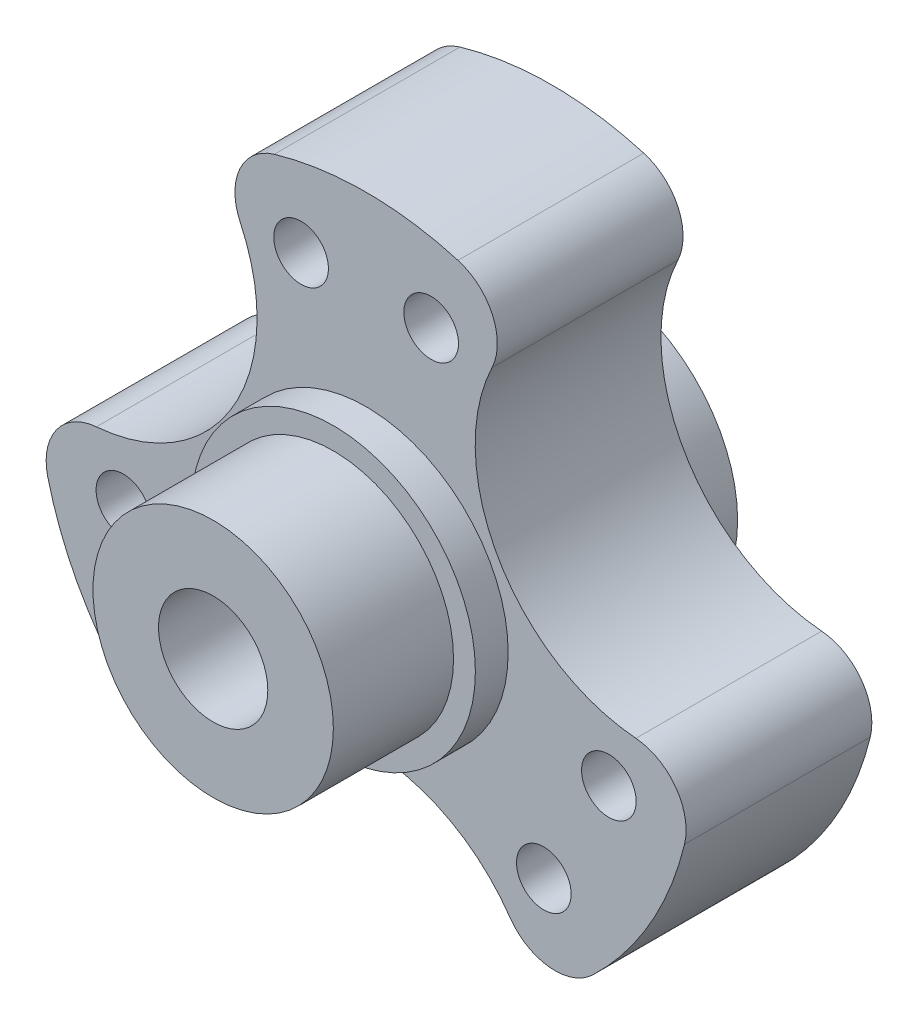
SolidWorks part; units mm, degrees
material "TIMETAL 35A CP 钛 (ASTM 等级 1) 99.1 Ti"
ref_plane "前视基准面" through (0, 0, 0) normal (0, 0, 1) x (1, 0, 0)
ref_plane "上视基准面" through (0, 0, 0) normal (0, 1, 0) x (1, 0, 0)
ref_plane "右视基准面" through (0, 0, 0) normal (1, 0, 0) x (0, 0, -1)
sketch "草图1" plane through (0, 0, 0) normal (0, 0, 1) x (1, 0, 0)
  line L0 (0, -38.5528) -> (0, 39.6388) construction
  line L1 (0, 0) -> (-10.2324, 38.188) construction
  line L2 (5.9528, 22.2163) -> (0, 0) construction
  circle A0 centre (0, 0) radius 23 construction
  circle A1 centre (-5.9528, 22.2163) radius 2.5
  circle A2 centre (0, 0) radius 30
  circle A3 centre (5.9528, 22.2163) radius 2.5
  circle A4 centre (22.2163, -5.9528) radius 2.5
  circle A5 centre (16.2635, -16.2635) radius 2.5
  circle A6 centre (-16.2635, -16.2635) radius 2.5
  circle A7 centre (-22.2163, -5.9528) radius 2.5
  point P22 (0, 0)
  dimension "D1" = 46
  dimension "D2" = 15
  dimension "D3" = 60
  dimension "D5" = 5
  dimension "D6" = 5
  dimension "D4" = 15
  dimension "D7" = 23
  dimension "D8" = 23
  dimension "D9" = 3
extrude "凸台-拉伸1" add sketch "草图1" along normal blind 17
sketch "草图2" plane through (0, 0, 17) normal (0, 0, 1) x (1, 0, 0)
  line L0 (0, 0) -> (25.9808, 15) construction
  line L1 (0, 0) -> (0, 30) construction
  circle A0 centre (0, 0) radius 30 construction
  circle A1 centre (25.9808, 15) radius 16
  dimension "D2" = 32
  dimension "D1" = 60
extrude "切除-拉伸1" cut sketch "草图2" against normal through all
pattern_circular "阵列(圆周)1" count 3 over 360 about axis through (0, 0, 0) along (0, 0, 1) of "切除-拉伸1"
sketch "草图4" plane through (0, 0, 17) normal (0, 0, 1) x (1, 0, 0)
  circle A0 centre (0, 0) radius 11
  dimension "D1" = 22
extrude "凸台-拉伸3" add sketch "草图4" along normal blind 14
sketch "草图5" plane through (0, 0, 31) normal (0, 0, 1) x (1, 0, 0)
  circle A0 centre (0, 0) radius 5
  dimension "D1" = 10
extrude "切除-拉伸2" cut sketch "草图5" against normal through all
sketch "草图6" plane through (0, 0, 31) normal (0, 0, 1) x (1, 0, 0)
  line L1 (-2, 6.25) -> (2, 6.25)
  line L2 (-2, 6.25) -> (-2, 3.75)
  line L3 (-2, 3.75) -> (2, 3.75)
  line L4 (2, 6.25) -> (2, 3.75)
  line L5 (-2, 6.25) -> (2, 3.75) construction
  line L6 (-2, 3.75) -> (2, 6.25) construction
  circle A0 centre (0, 0) radius 5 construction
  point P0 (0, 5)
  dimension "D1" = 4
  dimension "D2" = 2.5
extrude "切除-拉伸3" cut sketch "草图6" against normal through all
sketch "草图7" plane through (0, 0, 0) normal (0, 0, -1) x (-1, 0, 0)
  line L0 (-2, 4.5826) -> (-2, 6.25) construction
  line L1 (-2, 6.25) -> (2, 6.25) construction
  line L2 (2, 6.25) -> (2, 4.5826) construction
  line L3 (-2, 4.5826) -> (-2, 6.25)
  line L4 (-2, 6.25) -> (2, 6.25)
  line L5 (2, 6.25) -> (2, 4.5826)
  circle A0 centre (0, 0) radius 13
  arc A1 (-2, 4.5826) -> (2, 4.5826) centre (0, 0) ccw construction
  arc A2 (-2, 4.5826) -> (2, 4.5826) centre (0, 0) ccw
  dimension "D1" = 26
extrude "凸台-拉伸4" add sketch "草图7" along normal blind 4
sketch "草图8" plane through (0, 0, -4) normal (0, 0, -1) x (-1, 0, 0)
  line L0 (-2, 4.5826) -> (-2, 6.25)
  line L1 (-2, 6.25) -> (2, 6.25)
  line L2 (2, 6.25) -> (2, 4.5826)
  arc A0 (2, 4.5826) -> (-2, 4.5826) centre (0, 0) ccw
extrude "凸台-拉伸5" add sketch "草图8" against normal up to surface (35 mm away) up to face at (0, 3.0206, 31)
sketch "草图10" plane through (0, 0, 17) normal (0, 0, 1) x (1, 0, 0)
  circle A0 centre (0, 0) radius 11
  circle A1 centre (0, 0) radius 13
  dimension "D1" = 22
  dimension "D2" = 26
extrude "凸台-拉伸8" add sketch "草图10" along normal blind 3
fillet "圆角1" radius 5 6 edges at (-29.996, -0.488, 8.5) (-14.5754, 26.2213, 8.5) (14.5754, 26.2213, 8.5) (29.996, -0.488, 8.5) (15.4206, -25.7333, 8.5) (-15.4206, -25.7333, 8.5)
